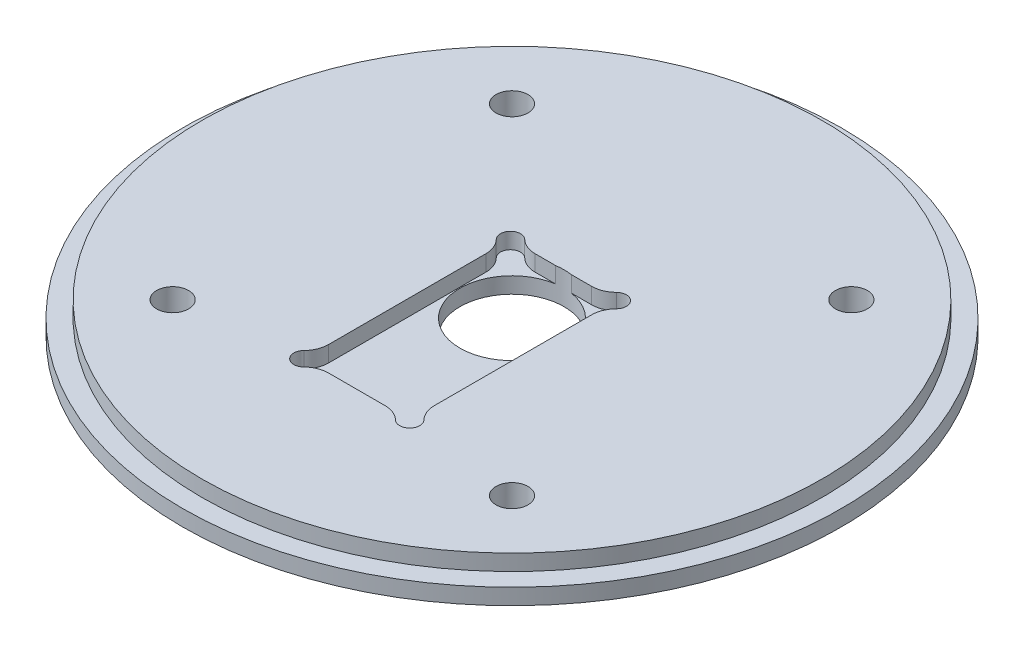
SolidWorks part; units mm, degrees
ref_plane "Front Plane" through (0, 0, 0) normal (0, 0, 1) x (1, 0, 0)
ref_plane "Top Plane" through (0, 0, 0) normal (0, 1, 0) x (1, 0, 0)
ref_plane "Right Plane" through (0, 0, 0) normal (1, 0, 0) x (0, 0, -1)
sketch "Sketch2" plane through (0, 0, 0) normal (0, 1, 0) x (1, 0, 0)
  circle A0 centre (0, 0) radius 65.405
  dimension "D1" = 130.81
extrude "Boss-Extrude1" add sketch "Sketch2" along normal blind 6.35
sketch "Sketch4" plane through (0, 6.35, 0) normal (0, 1, 0) x (1, 0, 0)
  circle A0 centre (0, 0) radius 61.595
  circle A1 centre (0, 0) radius 65.405 construction
  circle A2 centre (0, 0) radius 65.405
  dimension "D1" = 123.19
extrude "Cut-Extrude1" cut sketch "Sketch4" against normal blind 3.175
sketch "Sketch5" plane through (0, 6.35, 0) normal (0, 1, 0) x (1, 0, 0)
  line L0 (33.676, 33.676) -> (-33.676, -33.676) construction
  line L1 (-33.676, 33.676) -> (33.676, -33.676) construction
  line L2 (-1000, 0) -> (49000, 0) construction
  point P1 (-33.676, -33.676)
  point P2 (33.676, 33.676)
  point P5 (33.676, -33.676)
  point P6 (-33.676, 33.676)
  dimension "D1" = 95.25
  dimension "D2" = 45
hole_wizard "1/4 (0.25) Diameter Hole1" positions "Sketch5" profile "Sketch6" hole size "1/4" standard "ANSI Inch" end condition through all
sketch "Sketch6" plane through (-33.676, 6.35, -33.676) normal (1, 0, 0) x (0, 0, 1)
  line L0 (0, 0) -> (0, 6.35)
  line L1 (0, 6.35) -> (3.175, 6.35)
  line L2 (3.175, 6.35) -> (3.175, 0)
  line L5 (3.175, 0) -> (0, 0)
  line L11 (0, -6.35) -> (0, 107.95) construction
  dimension "Thru Hole Dia." = 6.35
  dimension "Thru Hole Depth" = 6.35
sketch "Sketch7" plane through (0, 6.35, 0) normal (0, 1, 0) x (1, 0, 0)
  point P0 (0, 0)
hole_wizard "13/16 (0.8125) Diameter Hole1" positions "Sketch7" profile "Sketch8" hole size "13/16" standard "ANSI Inch" end condition through all
sketch "Sketch8" plane through (0, 6.35, 0) normal (1, 0, 0) x (0, 0, 1)
  line L0 (0, 0) -> (0, 6.35)
  line L1 (0, 6.35) -> (10.3187, 6.35)
  line L2 (10.3187, 6.35) -> (10.3187, 0)
  line L5 (10.3187, 0) -> (0, 0)
  line L11 (0, -6.35) -> (0, 107.95) construction
  dimension "Thru Hole Dia." = 20.6375
  dimension "Thru Hole Depth" = 6.35
sketch "Sketch11" plane through (0, 6.35, 0) normal (0, 1, 0) x (1, 0, 0)
  line L0 (0, -3.4925) -> (0, 3.4925) construction
  line L1 (-5.601, 10.2) -> (5.601, 10.2)
  line L2 (-10.5, 5.301) -> (-10.5, -25.901)
  line L3 (-5.601, -30.8) -> (5.601, -30.8)
  line L4 (10.5, 5.301) -> (10.5, -25.901)
  line L5 (-10.5, 10.2) -> (10.5, -30.8) construction
  line L6 (-10.5, -30.8) -> (10.5, 10.2) construction
  line L7 (0, -10.3) -> (7.6415, -10.3) construction
  line L8 (-10.5, -30.8) -> (-8.5, -30.8) construction
  line L9 (-10.5, -28.8) -> (-10.5, -30.8) construction
  line L10 (-10.5, 10.2) -> (-8.5, 10.2) construction
  line L11 (-10.5, 10.2) -> (-10.5, 8.2) construction
  line L12 (8.5, -30.8) -> (10.5, -30.8) construction
  line L13 (10.5, -28.8) -> (10.5, -30.8) construction
  line L14 (8.5, 10.2) -> (10.5, 10.2) construction
  line L15 (10.5, 10.2) -> (10.5, 8.2) construction
  arc A0 (-11.9286, -29.4003) -> (-9.1003, -32.2286) centre (-10.5, -30.8) ccw
  arc A1 (11.9286, -29.4003) -> (9.1003, -32.2286) centre (10.5, -30.8) cw
  arc A2 (11.9286, 8.8003) -> (9.1003, 11.6286) centre (10.5, 10.2) ccw
  arc A3 (-11.9286, 8.8003) -> (-9.1003, 11.6286) centre (-10.5, 10.2) cw
  arc A4 (-11.9286, -29.4003) -> (-10.5, -25.901) centre (-15.5, -25.901) ccw
  arc A5 (-9.1003, -32.2286) -> (-5.601, -30.8) centre (-5.601, -35.8) cw
  arc A6 (11.9286, -29.4003) -> (10.5, -25.901) centre (15.5, -25.901) cw
  arc A7 (9.1003, -32.2286) -> (5.601, -30.8) centre (5.601, -35.8) ccw
  arc A8 (11.9286, 8.8003) -> (10.5, 5.301) centre (15.5, 5.301) ccw
  arc A9 (9.1003, 11.6286) -> (5.601, 10.2) centre (5.601, 15.2) cw
  arc A10 (-9.1003, 11.6286) -> (-5.601, 10.2) centre (-5.601, 15.2) ccw
  arc A11 (-11.9286, 8.8003) -> (-10.5, 5.301) centre (-15.5, 5.301) cw
  point P0 (0, 0)
  point P1 (0, -10.3)
  dimension "D4" = 2
  dimension "D5" = 5
  dimension "D1" = 10.2
  dimension "D2" = 21
  dimension "D3" = 41
extrude "Cut-Extrude3" cut sketch "Sketch11" against normal blind 3.175
sketch "Sketch9" plane through (0, 0, 0) normal (0, -1, 0) x (1, 0, 0)
  circle A0 centre (-33.676, -33.676) radius 3.175 construction
  circle A1 centre (33.676, -33.676) radius 3.175 construction
  circle A2 centre (33.676, 33.676) radius 3.175 construction
  circle A3 centre (-33.676, 33.676) radius 3.175 construction
  circle A4 centre (-33.676, -33.676) radius 3.175 construction
  circle A5 centre (33.676, -33.676) radius 3.175 construction
  circle A6 centre (33.676, 33.676) radius 3.175 construction
  circle A7 centre (-33.676, 33.676) radius 3.175 construction
  circle A8 centre (-33.676, 33.676) radius 6.0325
  circle A9 centre (33.676, 33.676) radius 6.0325
  circle A10 centre (33.676, -33.676) radius 6.0325
  circle A11 centre (-33.676, -33.676) radius 6.0325
  point P13 (-33.676, 33.676)
  point P14 (33.676, 33.676)
  point P15 (33.676, -33.676)
  point P16 (-33.676, -33.676)
  dimension "D1" = 12.065
extrude "Cut-Extrude2" cut sketch "Sketch9" against normal blind 1.5875
equation "\"AIRFRAME_OD\"= 5.15in"
equation "\"AIRFRAME_ID\"= 4.99in"
equation "\"FLAT_T\"= 0.125in"
equation "\"NOSE_EXP_L\"= 27in"
equation "\"NOSE_SHOULDER_L\"= 5in"
equation "\"MAIN_L\"= 30in"
equation "\"RECO_COUP_L\"= 10in"
equation "\"RECO_SWITCH_L\"= 2in"
equation "\"DROGUE_L\"= 20in"
equation "\"ATS_FORE_COUP_L\"= 5.5in"
equation "\"ATS_AFT_COUP_L\"= 4.5in"
equation "\"LOWER_L\"= 30in"
equation "\"FIN_N\"= 4"
equation "\"CR_AFT_X\"= 0.5in"
equation "\"CR_FORE_X\"= 9.25in"
equation "\"D1@Boss-Extrude1\"=2*\"FLAT_T\""
equation "\"COUPLER_OD\"= 4.998in"
equation "\"COUPLER_ID\"= 4.85in"
equation "\"RECO_ROD_X\"= 3.5in"
equation "\"ATS_ROD_X\"= 3.75in"
equation "\"FIN_ROOT\"= 8in"
equation "\"FIN_X\"= 0.75in"
equation "\"MOTOR_OD\"= 3.091in"
equation "\"MOTOR_ID\"= 3.00in"
equation "\"MOTOR_L\"= 14in"
equation "\"MOTOR_LOWER_X\"= 2in"
equation "\"D1@Sketch4\"=\"COUPLER_ID\""
equation "\"D1@Cut-Extrude1\"=\"FLAT_T\""
equation "\"D1@Cut-Extrude3\"=\"FLAT_T\""
equation "\"D1@Sketch2\"=\"AIRFRAME_OD\""
equation "\"D1@Sketch5\"=\"ATS_ROD_X\""
